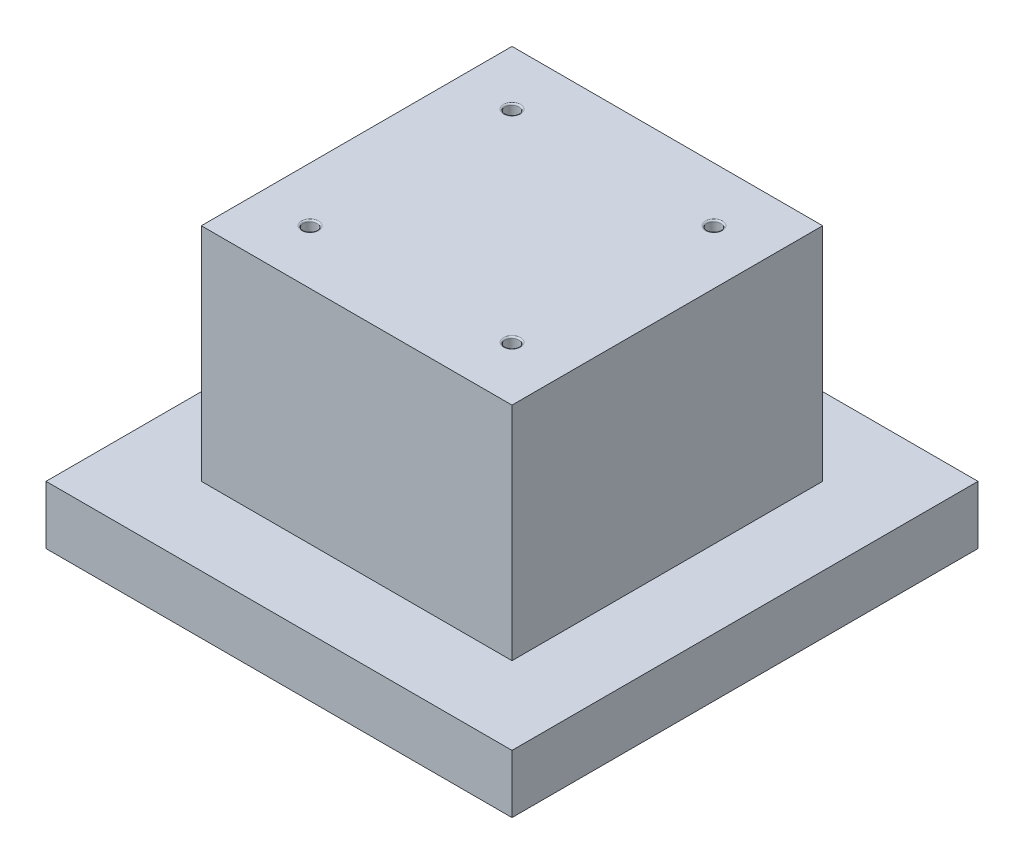
SolidWorks part; units mm, degrees
material "6061-T6 (SS)"
ref_plane "Front" through (0, 0, 0) normal (0, 0, 1) x (1, 0, 0)
ref_plane "Top" through (0, 0, 0) normal (0, 1, 0) x (1, 0, 0)
ref_plane "Right" through (0, 0, 0) normal (1, 0, 0) x (0, 0, -1)
sketch "Sketch1" plane through (0, 0, 0) normal (0, 1, 0) x (1, 0, 0)
  line L1 (-38.1, 38.1) -> (38.1, 38.1)
  line L2 (-38.1, 38.1) -> (-38.1, -38.1)
  line L3 (-38.1, -38.1) -> (38.1, -38.1)
  line L4 (38.1, 38.1) -> (38.1, -38.1)
  line L5 (-38.1, 38.1) -> (38.1, -38.1) construction
  line L6 (-38.1, -38.1) -> (38.1, 38.1) construction
  point P0 (0, 0)
  dimension "D1" = 38.1
  dimension "D2" = 38.1
extrude "Extrude1" add sketch "Sketch1" along normal blind 9.525
sketch "Sketch2" plane through (0, 0, 0) normal (0, -1, 0) x (1, 0, 0)
  line L1 (-38.1, 38.1) -> (38.1, 38.1) construction
  line L2 (-34.29, 34.29) -> (34.29, 34.29)
  line L3 (-34.29, 34.29) -> (-34.29, -34.29)
  line L4 (-34.29, -34.29) -> (34.29, -34.29)
  line L5 (34.29, 34.29) -> (34.29, -34.29)
  line L6 (-34.29, 34.29) -> (34.29, -34.29) construction
  line L7 (-34.29, -34.29) -> (34.29, 34.29) construction
  line L8 (-38.1, -38.1) -> (-38.1, 38.1) construction
  point P0 (0, 0)
  dimension "D1" = 3.81
  dimension "D2" = 3.81
extrude "Extrude2" cut sketch "Sketch2" against normal blind 0.7937
sketch "Sketch6" plane through (0, 9.525, 0) normal (0, 1, 0) x (1, 0, 0)
  line L1 (-25.4, 25.4) -> (25.4, 25.4)
  line L2 (-25.4, 25.4) -> (-25.4, -25.4)
  line L3 (-25.4, -25.4) -> (25.4, -25.4)
  line L4 (25.4, 25.4) -> (25.4, -25.4)
  line L5 (-25.4, 25.4) -> (25.4, -25.4) construction
  line L6 (-25.4, -25.4) -> (25.4, 25.4) construction
  point P0 (0, 0)
  dimension "D1" = 50.8
  dimension "D2" = 50.8
extrude "Extrude4" add sketch "Sketch6" along normal blind 36.195
sketch "Sketch7" plane through (0, 45.72, 0) normal (0, 1, 0) x (1, 0, 0)
  line L1 (-16.51, 16.51) -> (16.51, 16.51)
  line L2 (-16.51, 16.51) -> (-16.51, -16.51)
  line L3 (-16.51, -16.51) -> (16.51, -16.51)
  line L4 (16.51, 16.51) -> (16.51, -16.51)
  line L5 (-16.51, 16.51) -> (16.51, -16.51) construction
  line L6 (-16.51, -16.51) -> (16.51, 16.51) construction
  point P0 (0, 0)
  dimension "D1" = 33.02
  dimension "D2" = 33.02
hole_wizard "#4-40 Tapped Hole1" positions "3DSketch1" profile "Sketch8" tap size "#4-40" standard "ANSI Inch"
sketch3d "3DSketch1"
  point P0 (-16.51, 45.72, -16.51)
  point P3 (-16.51, 45.72, 16.51)
  point P6 (16.51, 45.72, 16.51)
  point P9 (16.51, 45.72, -16.51)
sketch "Sketch8" plane through (-16.51, 45.72, -16.51) normal (1, 0, 0) x (0, 0, 1)
  line L0 (0, 0) -> (0, 13.3792)
  line L1 (0, 13.3792) -> (1.1303, 12.7)
  line L2 (1.1303, 12.7) -> (1.1303, 0)
  line L5 (1.1303, 0) -> (0, 0)
  line L10 (0, 13.3792) -> (-1.1303, 12.7) construction
  line L11 (0, -6.35) -> (0, 107.95) construction
  dimension "Tap Drill Dia." = 2.2606
  dimension "Tap Drill Depth" = 12.7
  dimension "Drill Angle" = 118
cosmetic thread "Hole Thread1" parameters "D1"=10.7696, "D2"=2.8448
cosmetic thread "Hole Thread2" parameters "D1"=10.7696, "D2"=2.8448
cosmetic thread "Hole Thread3" parameters "D1"=10.7696, "D2"=2.8448
cosmetic thread "Hole Thread4" parameters "D1"=10.7696, "D2"=2.8448
fillet "Fillet1" radius 0.254 4 edges at (16.51, 45.72, 17.6403) (16.51, 45.72, -15.3797) (-16.51, 45.72, -15.3797) (-16.51, 45.72, 17.6403)
